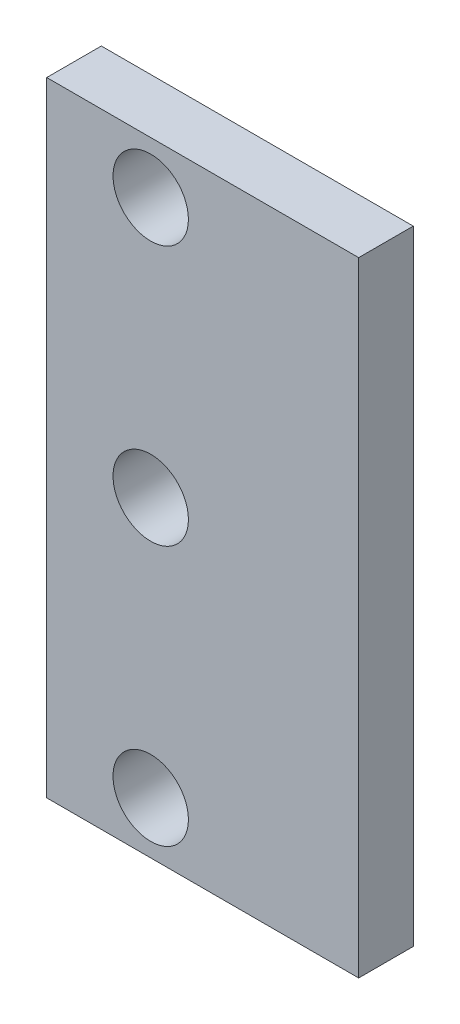
SolidWorks part; units mm, degrees
ref_plane "정면" through (0, 0, 0) normal (0, 0, 1) x (1, 0, 0)
ref_plane "윗면" through (0, 0, 0) normal (0, 1, 0) x (1, 0, 0)
ref_plane "우측면" through (0, 0, 0) normal (1, 0, 0) x (0, 0, -1)
sketch "스케치1" plane through (0, 0, 0) normal (0, 0, 1) x (1, 0, 0)
  line L1 (15, -30) -> (-15, -30)
  line L2 (15, -30) -> (15, 30)
  line L3 (15, 30) -> (-15, 30)
  line L4 (-15, -30) -> (-15, 30)
  line L5 (15, -30) -> (-15, 30) construction
  line L6 (15, 30) -> (-15, -30) construction
  circle A0 centre (-5, 25) radius 3.625
  circle A1 centre (-5, 0) radius 3.625
  circle A2 centre (-5, -25) radius 3.625
  point P0 (0, 0)
  point P12 (0, 0)
  point P13 (0, 0)
  dimension "D3" = 7.25
  dimension "D1" = 30
  dimension "D2" = 10
  dimension "D4" = 25
  dimension "D5" = 25
  dimension "D6" = 60
extrude "보스-돌출1" add sketch "스케치1" along normal blind 5.25
